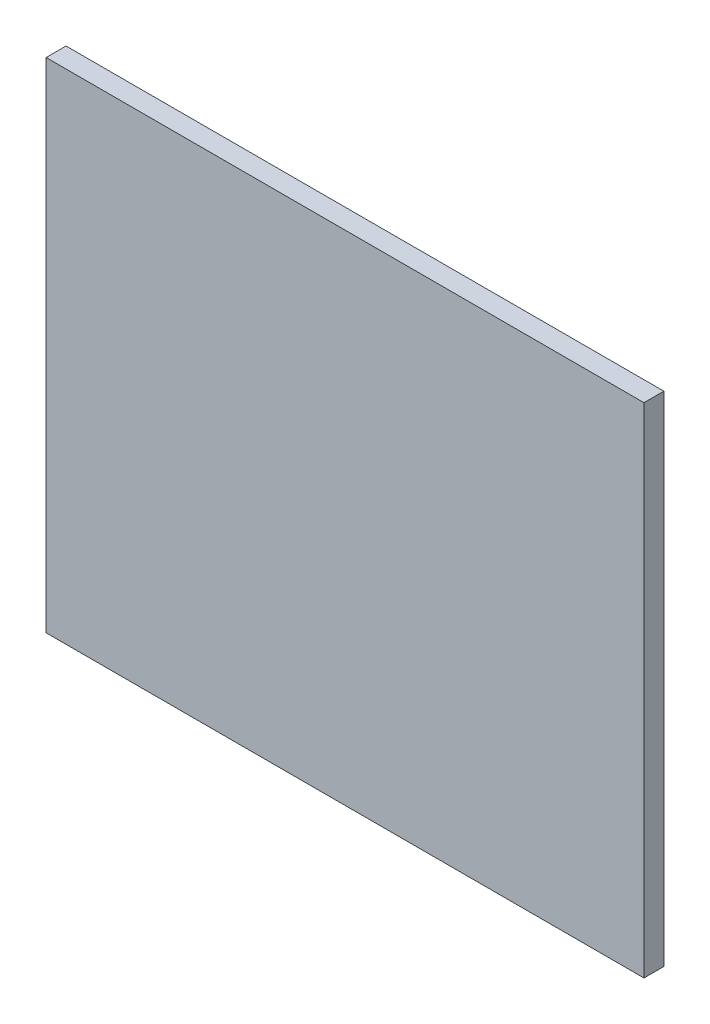
SolidWorks part; units mm, degrees
ref_plane "Front Plane" through (0, 0, 0) normal (0, 0, 1) x (1, 0, 0)
ref_plane "Top Plane" through (0, 0, 0) normal (0, 1, 0) x (1, 0, 0)
ref_plane "Right Plane" through (0, 0, 0) normal (1, 0, 0) x (0, 0, -1)
sketch "Sketch1" plane through (0, 0, 0) normal (0, 0, 1) x (1, 0, 0)
  line L1 (0, 0) -> (150, 0)
  line L2 (0, 0) -> (0, 125)
  line L3 (0, 125) -> (150, 125)
  line L4 (150, 0) -> (150, 125)
  dimension "D1" = 150
  dimension "D2" = 125
extrude "Boss-Extrude1" add sketch "Sketch1" against normal blind 5
sketch "Sketch2" plane through (0, 0, 0) normal (0, 0, 1) x (1, 0, 0)
  line L0 (0, 0) -> (150, 0) construction
  line L1 (150, 0) -> (150, 125) construction
  line L2 (0, 125) -> (0, 0) construction
  circle A0 centre (25, 12.5) radius 1.25
  circle A1 centre (125, 12.5) radius 1.25
  dimension "D1" = 2.5
  dimension "D2" = 2.5
  dimension "D4" = 12.5
  dimension "D3" = 12.5
  dimension "D5" = 25
  dimension "D6" = 25
extrude "Cut-Extrude1" [suppressed] cut sketch "Sketch2" against normal through all
sketch "Sketch3" plane through (0, 0, 0) normal (0, 0, 1) x (1, 0, 0)
  line L0 (150, 125) -> (0, 125) construction
  line L1 (0, 125) -> (0, 0) construction
  line L2 (150, 0) -> (150, 125) construction
  circle A0 centre (35, 117) radius 1.25
  circle A1 centre (115, 117) radius 1.25
  dimension "D1" = 2.5
  dimension "D2" = 2.5
  dimension "D3" = 8
  dimension "D4" = 35
  dimension "D5" = 35
  dimension "D6" = 8
extrude "Cut-Extrude2" [suppressed] cut sketch "Sketch3" against normal through all
sketch "Sketch4" plane through (0, 0, 0) normal (0, 0, 1) x (1, 0, 0)
  line L0 (150, 125) -> (0, 125) construction
  line L1 (0, 0) -> (150, 0) construction
  line L3 (150, 0) -> (150, 125) construction
  circle A0 centre (133.5, 90) radius 1.25
  circle A1 centre (133.5, 35) radius 1.25
  dimension "D1" = 2.5
  dimension "D2" = 2.5
  dimension "D3" = 35
  dimension "D4" = 35
  dimension "D5" = 16.5
  dimension "D6" = 16.5
extrude "Cut-Extrude3" [suppressed] cut sketch "Sketch4" against normal through all
